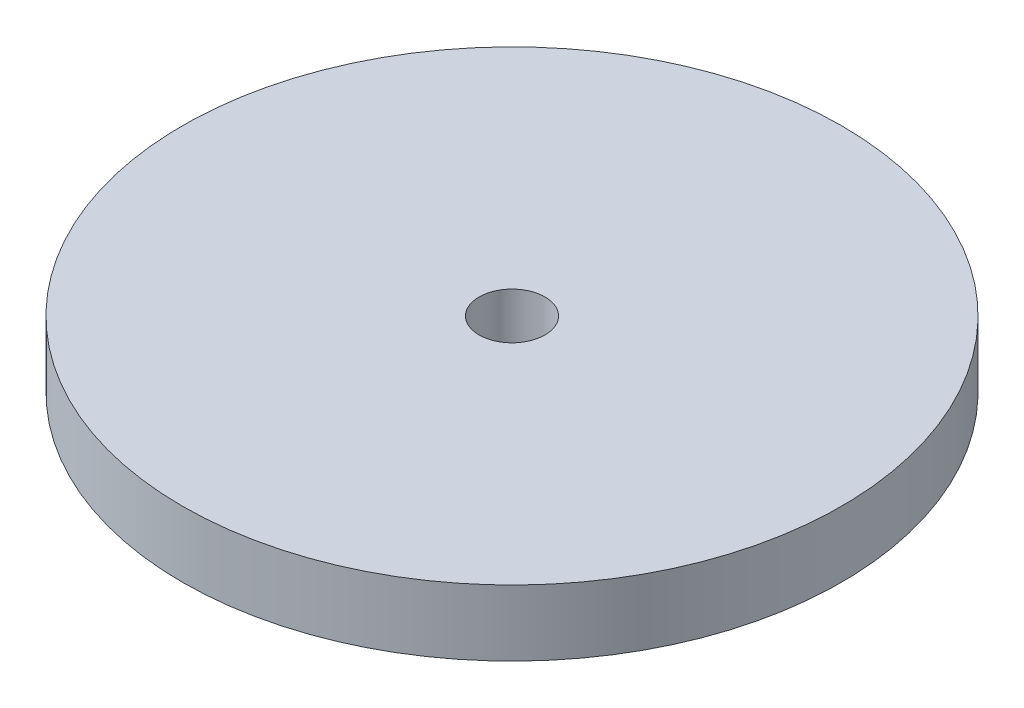
SolidWorks part; units mm, degrees
material "Plain Carbon Steel"
ref_plane "Front Plane" through (0, 0, 0) normal (0, 0, 1) x (1, 0, 0)
ref_plane "Top Plane" through (0, 0, 0) normal (0, 1, 0) x (1, 0, 0)
ref_plane "Right Plane" through (0, 0, 0) normal (1, 0, 0) x (0, 0, -1)
sketch "Sketch1" plane through (0, 0, 0) normal (0, 1, 0) x (1, 0, 0)
  circle A0 centre (0, 0) radius 5
  circle A1 centre (0, 0) radius 50
  dimension "D1" = 10
  dimension "D2" = 100
extrude "Boss-Extrude1" add sketch "Sketch1" along normal blind 10
